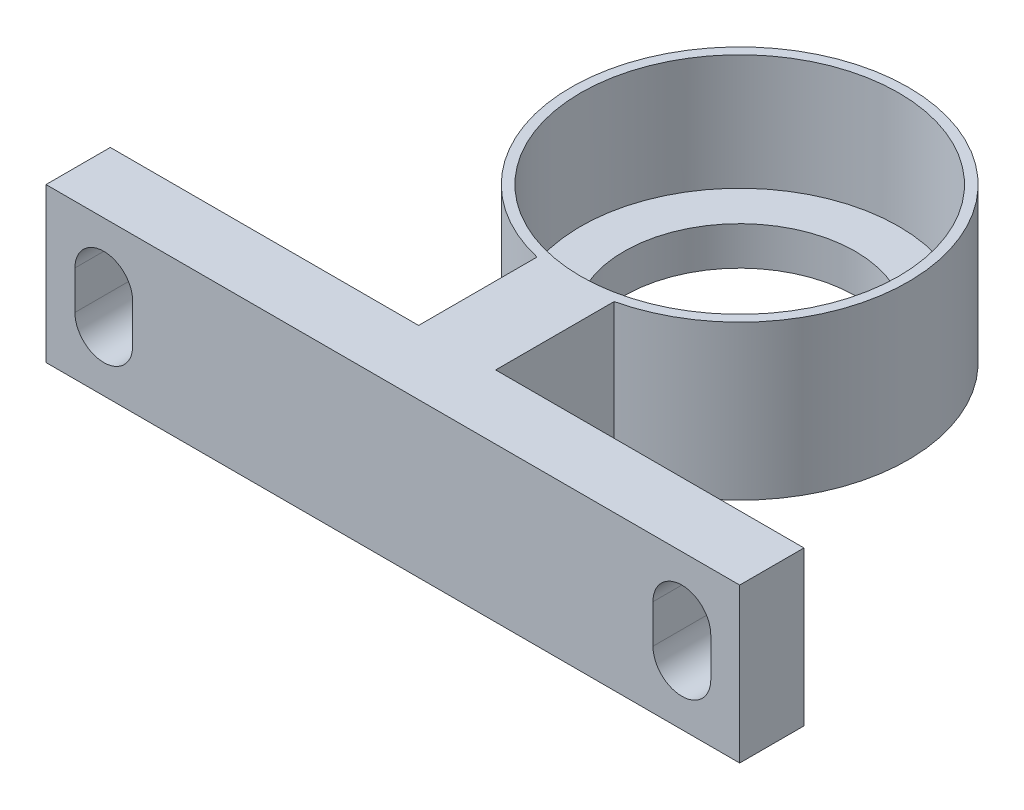
SolidWorks part; units mm, degrees
ref_plane "前视基准面" through (0, 0, 0) normal (0, 0, 1) x (1, 0, 0)
ref_plane "上视基准面" through (0, 0, 0) normal (0, 1, 0) x (1, 0, 0)
ref_plane "右视基准面" through (0, 0, 0) normal (1, 0, 0) x (0, 0, -1)
sketch "草图1" plane through (0, 0, 0) normal (0, 1, 0) x (1, 0, 0)
  circle A0 centre (0, 0) radius 8.25
  circle A1 centre (0, 0) radius 8.75
  dimension "D1" = 16.5
  dimension "D2" = 17.5
extrude "凸台-拉伸2" add sketch "草图1" along normal blind 10
sketch "草图2" plane through (0, 0, 0) normal (0, 1, 0) x (1, 0, 0)
  circle A0 centre (0, 0) radius 8.25
  circle A1 centre (0, 0) radius 2
  dimension "D1" = 4
extrude "凸台-拉伸3" add sketch "草图2" along normal blind 4
sketch "草图3" plane through (0, 0, 0) normal (0, 1, 0) x (1, 0, 0)
  line L0 (-2, 8.5184) -> (2, 8.5184)
  line L1 (-15, 18) -> (-15, 15)
  line L2 (2, 18) -> (15, 18)
  line L3 (-2, 8.5184) -> (-2, 15)
  line L4 (2, 8.5184) -> (2, 15)
  line L5 (-15, 18) -> (-2, 18)
  line L6 (-15, 15) -> (-2, 15)
  line L7 (15, 15) -> (15, 18)
  line L8 (2, 15) -> (15, 15)
  line L9 (2, 18) -> (-2, 18)
  circle A2 centre (0, 0) radius 8.75 construction
  dimension "D1" = 13
  dimension "D2" = 13
  dimension "D3" = 3
  dimension "D4" = 3
extrude "凸台-拉伸4" add sketch "草图3" along normal blind 8
sketch "草图5" plane through (15, 0, 0) normal (1, 0, 0) x (0, 0, -1)
  line L0 (15, 8) -> (18, 8)
  line L1 (15, 8) -> (15, 0)
  line L2 (18, 8) -> (18, 0)
  line L3 (15, 0) -> (18, 0)
  dimension "D1" = 8
extrude "凸台-拉伸5" add sketch "草图5" along normal blind 3
sketch "草图6" plane through (-15, 0, 0) normal (-1, 0, 0) x (0, 0, 1)
  line L0 (-18, 8) -> (-15, 8)
  line L1 (-18, 8) -> (-18, 0)
  line L2 (-15, 8) -> (-15, 0)
  line L3 (-18, 0) -> (-15, 0)
  dimension "D1" = 8
extrude "凸台-拉伸6" add sketch "草图6" along normal blind 3
sketch "草图7" plane through (0, 0, -18) normal (0, 0, -1) x (-1, 0, 0)
  circle A0 centre (-15, 3.754) radius 1.5
  dimension "D2" = 3
extrude "切除-拉伸1" cut sketch "草图7" against normal blind 3
mirror "镜向1" about plane through (0, 0, 0) normal (1, 0, 0) of "切除-拉伸1"
fillet "圆角1" radius 5 2 edges at (2, 4, -8.5184) (-2, 4, -8.5184)
fillet "圆角3" radius 2 2 edges at (-2, 4, -15) (2, 4, -15)
ref_plane "基准面1" through (0, 0, 10) normal (0, 0, 1) x (1, 0, 0)
sketch "草图8" plane through (0, 0, 0) normal (0, 1, 0) x (1, 0, 0)
  circle A0 centre (27.185, 0) radius 8.75
  circle A1 centre (27.185, 0) radius 8.25
  dimension "D1" = 17.5
  dimension "D2" = 16.5
extrude "凸台-拉伸7" add sketch "草图8" along normal blind 8 separate body
sketch "草图9" plane through (0, 0, 0) normal (0, -1, 0) x (1, 0, 0)
  circle A0 centre (27.185, 0) radius 8.25
  circle A1 centre (27.185, 0) radius 6
  dimension "D1" = 12
extrude "凸台-拉伸8" add sketch "草图9" against normal blind 2
sketch "草图10" plane through (0, 0, 0) normal (0, 1, 0) x (1, 0, 0)
  line L1 (27.185, -18) -> (45.185, -18)
  line L2 (27.185, -18) -> (9.185, -18)
  line L3 (9.185, -18) -> (9.185, -14.6639)
  line L4 (9.185, -14.6639) -> (25.185, -14.6639)
  line L5 (45.185, -18) -> (45.185, -14.6639)
  line L6 (45.185, -14.6639) -> (29.185, -14.6639)
  line L7 (25.185, -14.6639) -> (25.185, -8.5184)
  line L8 (25.185, -8.5184) -> (29.185, -8.5184)
  line L9 (29.185, -8.5184) -> (29.185, -14.6639)
  circle A0 centre (27.185, 0) radius 8.75 construction
  dimension "D2" = 18
  dimension "D3" = 18
  dimension "D4" = 16
  dimension "D5" = 16
extrude "凸台-拉伸9" add sketch "草图10" along normal blind 8
sketch "草图11" plane through (0, 0, 18) normal (0, 0, 1) x (1, 0, 0)
  circle A0 centre (12.185, 4) radius 1.5
  circle A1 centre (42.185, 4) radius 1.5
  dimension "D3" = 3
  dimension "D4" = 3
  dimension "D2" = 30
extrude "切除-拉伸2" cut sketch "草图11" against normal blind 8
sketch "草图12" plane through (0, 0, 18) normal (0, 0, 1) x (1, 0, 0)
  line L0 (10.685, 4) -> (10.685, 5)
  line L1 (13.685, 4) -> (13.685, 5)
  line L2 (10.685, 4) -> (10.685, 3)
  line L3 (13.685, 4) -> (13.685, 3)
  circle A0 centre (12.185, 4) radius 1.5 construction
  arc A1 (13.685, 5) -> (10.685, 5) centre (12.185, 5) ccw
  arc A2 (10.685, 3) -> (13.685, 3) centre (12.185, 3) ccw
  dimension "D1" = 1
  dimension "D2" = 1
  dimension "D3" = 1
  dimension "D4" = 1
extrude "切除-拉伸3" cut sketch "草图12" against normal blind 8
sketch "草图13" plane through (0, 0, 18) normal (0, 0, 1) x (1, 0, 0)
  line L0 (40.685, 4) -> (40.685, 5)
  line L2 (43.685, 5) -> (43.685, 4)
  line L3 (43.685, 4) -> (43.685, 3)
  line L5 (40.685, 3) -> (40.685, 4)
  circle A0 centre (42.185, 4) radius 1.5 construction
  arc A1 (43.685, 5) -> (40.685, 5) centre (42.185, 5) ccw
  arc A2 (40.685, 3) -> (43.685, 3) centre (42.185, 3) ccw
  dimension "D1" = 1
  dimension "D2" = 1
  dimension "D3" = 1
extrude "切除-拉伸4" cut sketch "草图13" against normal blind 8
sketch "草图14" plane through (0, 0, 0) normal (0, 1, 0) x (1, 0, 0)
  circle A0 centre (-35.0916, 0) radius 8.75
  circle A1 centre (-35.0916, 0) radius 8.25
  dimension "D1" = 17.5
  dimension "D2" = 16.5
extrude "凸台-拉伸10" add sketch "草图14" along normal blind 8 separate body
sketch "草图15" plane through (0, 0, 0) normal (0, 1, 0) x (1, 0, 0)
  line L0 (-37.0916, -15) -> (-37.0916, -8.5184)
  line L2 (-17.0916, -18) -> (-53.0916, -18)
  line L3 (-53.0916, -18) -> (-53.0916, -15)
  line L4 (-53.0916, -15) -> (-37.0916, -15)
  line L5 (-37.0916, -8.5184) -> (-33.0916, -8.5184)
  line L6 (-33.0916, -15) -> (-17.0916, -15)
  line L7 (-17.0916, -15) -> (-17.0916, -18)
  line L8 (-33.0916, -8.5184) -> (-33.0916, -15)
  circle A0 centre (-35.0916, 0) radius 8.75 construction
  dimension "D4" = 3
  dimension "D5" = 16
  dimension "D6" = 16
extrude "凸台-拉伸11" add sketch "草图15" along normal blind 8
sketch "草图16" plane through (0, 0, 18) normal (0, 0, 1) x (1, 0, 0)
  circle A0 centre (-50.0916, 4) radius 1.5
  circle A1 centre (-20.0916, 4) radius 1.5
  dimension "D3" = 3
  dimension "D4" = 3
extrude "切除-拉伸5" cut sketch "草图16" against normal blind 8
sketch "草图17" plane through (0, 0, 0) normal (0, 1, 0) x (1, 0, 0)
  line L0 (-27.7246, 21.696) -> (-7.3492, -14.3382)
  line L1 (-7.3492, -14.3382) -> (7.1777, -11.697)
  line L2 (7.1777, -11.697) -> (13.5921, 5.6598)
  line L3 (13.5921, 5.6598) -> (24.1571, 16.0362)
  line L4 (24.1571, 16.0362) -> (2.4672, 27.5538)
  line L5 (2.4672, 27.5538) -> (0, 27.5538)
  line L6 (-27.7246, 21.696) -> (0, 27.5538)
extrude "切除-拉伸6" cut sketch "草图17" along normal blind 10
sketch "草图18" plane through (0, 0, 0) normal (0, 1, 0) x (1, 0, 0)
  line L0 (-5.3343, 26.5426) -> (-7.1079, -29.6533)
  line L1 (-7.1079, -29.6533) -> (-79.0093, -22.654)
  line L2 (-79.0093, -22.654) -> (-79.0093, -19.0854)
  line L3 (-48.1997, 26.5426) -> (-79.0093, -19.0854)
  line L4 (-5.3343, 26.5426) -> (-48.1997, 26.5426)
extrude "切除-拉伸7" cut sketch "草图18" along normal blind 10
